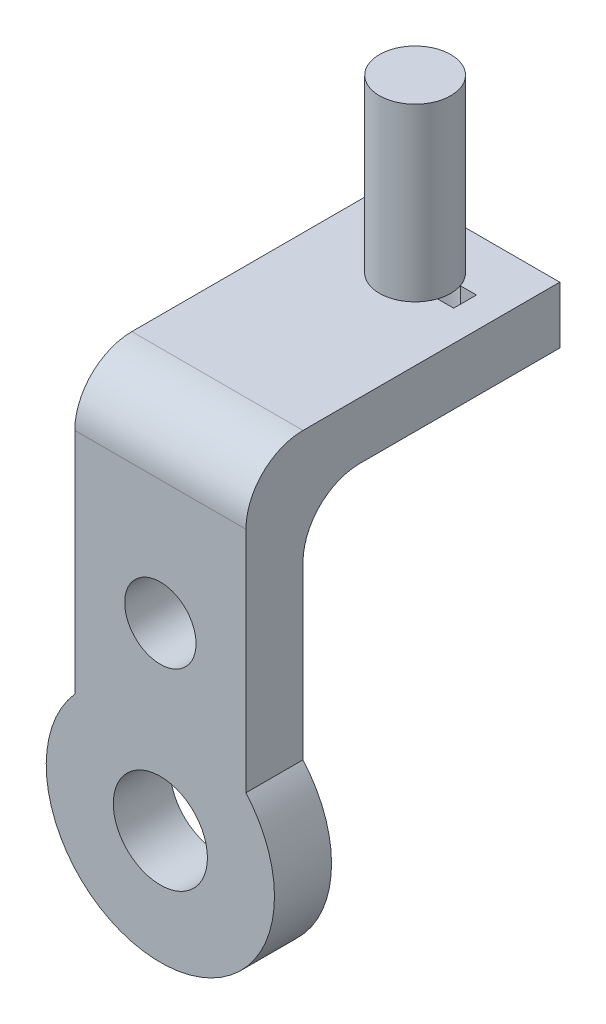
SolidWorks part; units mm, degrees
ref_plane "Front Plane" through (0, 0, 0) normal (0, 0, 1) x (1, 0, 0)
ref_plane "Top Plane" through (0, 0, 0) normal (0, 1, 0) x (1, 0, 0)
ref_plane "Right Plane" through (0, 0, 0) normal (1, 0, 0) x (0, 0, -1)
sketch "Sketch1" plane through (0, 0, 0) normal (0, 0, 1) x (1, 0, 0)
  line L0 (33.2298, -31.9802) -> (33.2673, -31.9802)
  line L1 (-26.7327, 68.0198) -> (33.2673, 68.0198)
  line L2 (-26.7327, 68.0198) -> (-26.7327, -31.9802)
  line L3 (-26.7327, -31.9802) -> (-26.6951, -31.9802)
  line L4 (33.2673, 68.0198) -> (33.2673, -31.9802)
  circle A0 centre (3.2673, -58.4802) radius 16.5
  arc A1 (-26.6951, -31.9802) -> (33.2298, -31.9802) centre (3.2673, -58.4802) ccw
  dimension "D3" = 33
  dimension "D5" = 80
  dimension "D1" = 60
  dimension "D2" = 100
  dimension "D4" = 26.5
extrude "Boss-Extrude1" add sketch "Sketch1" along normal blind 20
sketch "Sketch2" plane through (0, 0, 0) normal (0, 0, -1) x (-1, 0, 0)
  line L0 (26.7327, 68.0198) -> (26.7327, -31.9802) construction
  line L1 (-33.2673, 68.0198) -> (26.7327, 68.0198)
  line L2 (-33.2673, 68.0198) -> (-33.2673, 48.0198)
  line L3 (-33.2673, 48.0198) -> (26.7327, 48.0198)
  line L4 (26.7327, 68.0198) -> (26.7327, 48.0198)
  dimension "D1" = 20
extrude "Boss-Extrude3" add sketch "Sketch2" along normal blind 90
fillet "Fillet2" radius 20 1 edges at (3.2673, 68.0198, 20)
fillet "Fillet3" radius 20 1 edges at (3.2673, 48.0198, 0)
sketch "Sketch3" plane through (0, 68.0198, 0) normal (0, 1, 0) x (1, 0, 0)
  line L0 (-26.7327, 90) -> (33.2673, 90) construction
  line L2 (16.9033, 71.5) -> (22.5606, 71.5)
  line L4 (16.9033, 63.5) -> (22.5606, 63.5)
  line L5 (22.5606, 71.5) -> (22.5606, 63.5)
  line L6 (17.5606, 67.5) -> (22.5606, 63.5) construction
  line L7 (17.5606, 67.5) -> (22.5606, 71.5) construction
  arc A0 (16.9033, 71.5) -> (16.9033, 63.5) centre (5.0606, 67.5) ccw
  point P4 (17.5606, 67.5)
  dimension "D1" = 25
  dimension "D2" = 22.5
extrude "Cut-Extrude1" cut sketch "Sketch3" against normal through all
sketch "Sketch4" plane through (0, 0, 20) normal (0, 0, 1) x (1, 0, 0)
  line L0 (3.2673, -58.4802) -> (3.2673, 4.5198)
  circle A0 centre (3.2673, -58.4802) radius 26.5
  circle A1 centre (3.2673, 4.5198) radius 12.5
  dimension "D2" = 25
  dimension "D1" = 63
extrude "Cut-Extrude4" cut sketch "Sketch4" against normal blind 25
sketch "Sketch5" plane through (0, 68.0198, 0) normal (0, 1, 0) x (1, 0, 0)
  circle A0 centre (5.0606, 67.5) radius 12.5
  dimension "D1" = 25
extrude "Boss-Extrude4" add sketch "Sketch5" along normal blind 60 separate body
